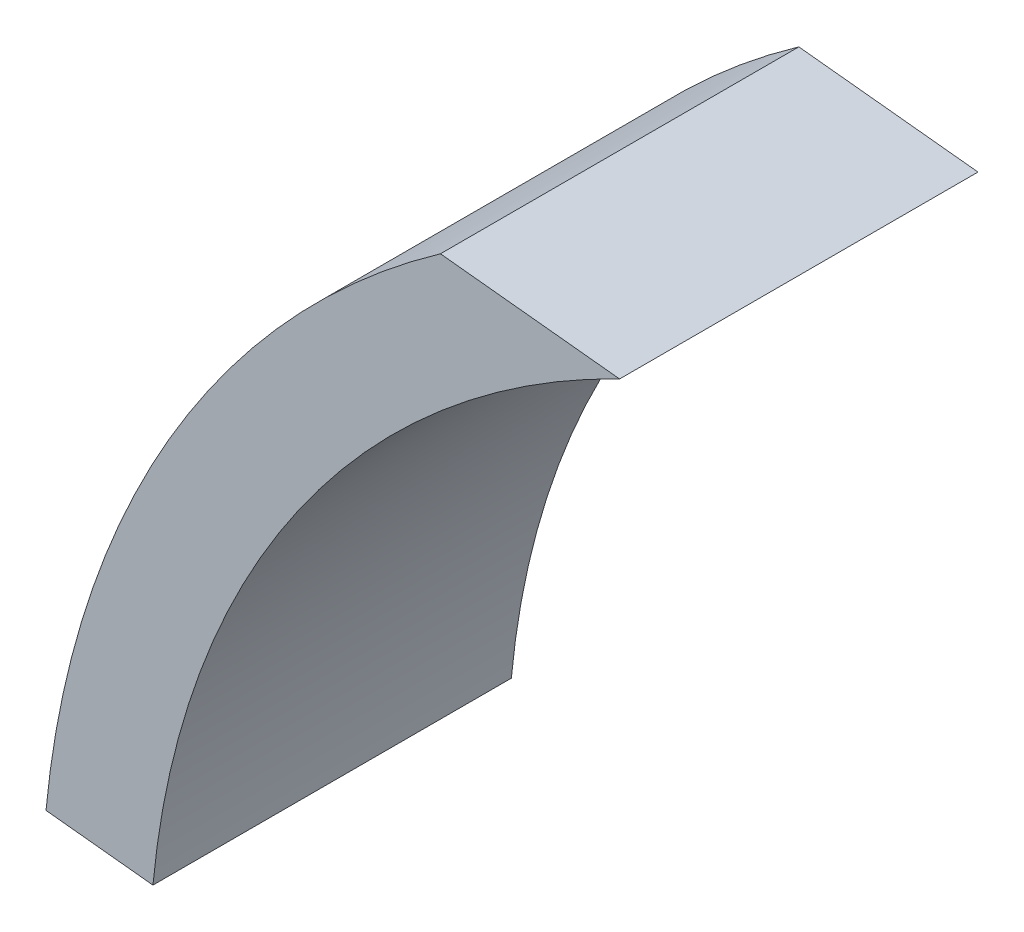
SolidWorks part; units mm, degrees
ref_plane "前视基准面" through (0, 0, 0) normal (0, 0, 1) x (1, 0, 0)
ref_plane "上视基准面" through (0, 0, 0) normal (0, 1, 0) x (1, 0, 0)
ref_plane "右视基准面" through (0, 0, 0) normal (1, 0, 0) x (0, 0, -1)
other "Configuration Table"
sketch "草图1" plane through (0, 0, 0) normal (0, 0, 1) x (1, 0, 0)
  line L0 (-9.3, 0) -> (-10.5, 0)
  line L1 (0, 0) -> (5.25, 0) construction
  line L2 (0, 0) -> (10.4425, 1.0975) construction
  line L3 (10.4425, 1.0975) -> (9.2491, 0.9721)
  arc A0 (9.2491, 0.9721) -> (-9.3, 0) centre (0, 0) ccw
  arc A1 (10.4425, 1.0975) -> (-10.5, 0) centre (0, 0) ccw
  dimension "D1" = 18.6
  dimension "D2" = 21
  dimension "D3" = 6
extrude "凸台-拉伸1" add sketch "草图1" along normal blind 6.15
sketch "草图2" plane through (0, 0, 6.15) normal (0, 0, 1) x (1, 0, 0)
  line L0 (0, 0) -> (4.6729, 0)
  line L1 (0, 0) -> (9.2491, 0.9721)
  line L2 (0, 0) -> (-9.3, 0)
  line L3 (0, 0) -> (-9.2491, 0.9721)
  arc A0 (9.2491, 0.9721) -> (-9.3, 0) centre (0, 0) ccw construction
  dimension "D1" = 6
ref_plane "基准面1" through (0, 0, 6.15) normal (0.9945, 0.1045, 0) x (0, 0, -1)
ref_plane "基准面2" through (0, 0, 6.15) normal (-0.9945, 0.1045, 0) x (0, 0, 1)
sketch "草图4" plane through (0, 0, 6.15) normal (-0.9945, 0.1045, 0) x (0, 0, 1)
  line L1 (0, -0.0975) -> (-4, -0.0975)
  line L3 (0, 7.9025) -> (-4, 7.9025)
  line L4 (-4, -0.0975) -> (-4, 7.9025)
  line L7 (0, -1.0975) -> (-6.15, -1.0975) construction
  line L8 (0, 7.9025) -> (0, 10.5)
  line L9 (0, -1.0975) -> (-6.15, -1.0975)
  line L10 (0, -1.0975) -> (0, -0.0975)
  line L11 (0, 10.5) -> (-6.15, 10.5)
  line L12 (-6.15, -1.0975) -> (-6.15, 10.5)
  dimension "D1" = 1
  dimension "D2" = 8
  dimension "D3" = 4
extrude "切除-拉伸1" cut sketch "草图4" against normal through all both and the other way through all
